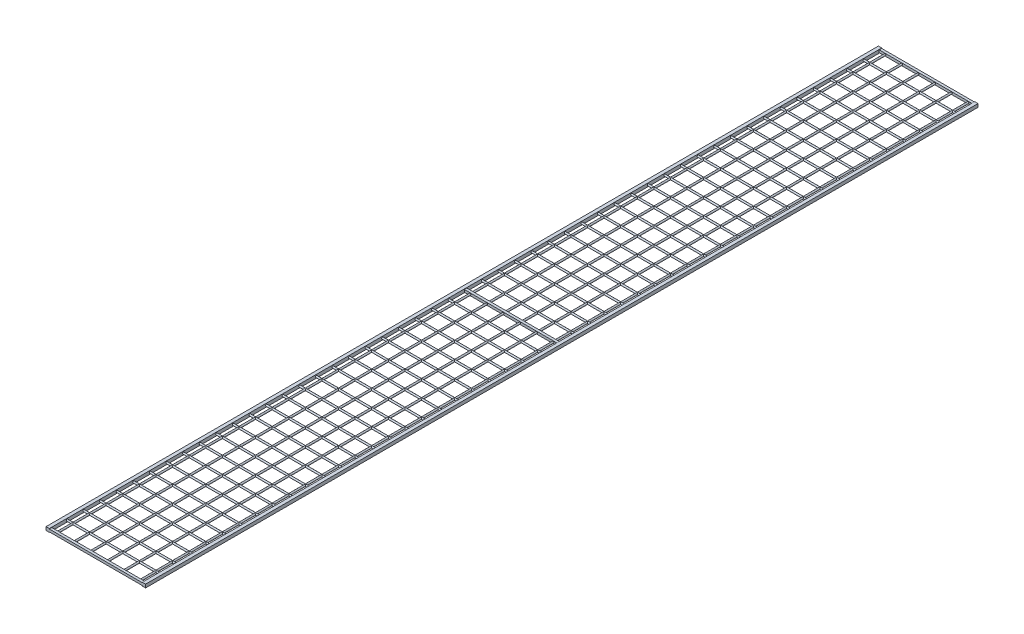
SolidWorks part; units mm, degrees
ref_plane "Piano frontale" through (0, 0, 0) normal (0, 0, 1) x (1, 0, 0)
ref_plane "Piano superiore" through (0, 0, 0) normal (0, 1, 0) x (1, 0, 0)
ref_plane "Piano destro" through (0, 0, 0) normal (1, 0, 0) x (0, 0, -1)
sketch "Schizzo2" plane through (0, 0, 0) normal (0, 0, 1) x (1, 0, 0)
  line L0 (0, 0) -> (5.716, 0) construction
  line L1 (0, 0) -> (50, 0) construction
  circle A0 centre (0, 0) radius 2.5
  circle A1 centre (50, 0) radius 2.5
  circle A2 centre (100, 0) radius 2.5
  circle A3 centre (150, 0) radius 2.5
  circle A4 centre (200, 0) radius 2.5
  circle A5 centre (250, 0) radius 2.5
  circle A6 centre (300, 0) radius 2.5
  circle A7 centre (350, 0) radius 2.5
  circle A8 centre (400, 0) radius 2.5
  circle A9 centre (450, 0) radius 2.5
  circle A10 centre (500, 0) radius 2.5
  circle A11 centre (550, 0) radius 2.5
  circle A12 centre (600, 0) radius 2.5
  circle A13 centre (650, 0) radius 2.5
  circle A14 centre (700, 0) radius 2.5
  circle A15 centre (750, 0) radius 2.5
  circle A16 centre (800, 0) radius 2.5
  circle A17 centre (850, 0) radius 2.5
  circle A18 centre (900, 0) radius 2.5
  dimension "D1" = 50
  dimension "D2" = 19
extrude "Estrusione-Estrusione1" add sketch "Schizzo2" along normal blind 2500 contours A0
sketch "Schizzo3" plane through (0, 0, 0) normal (1, 0, 0) x (0, 0, -1)
  line L0 (0, 0) -> (-50, 0) construction
  circle A0 centre (0, 0) radius 2.5
  circle A1 centre (-50, 0) radius 2.5
  circle A2 centre (-100, 0) radius 2.5
  circle A3 centre (-150, 0) radius 2.5
  circle A4 centre (-200, 0) radius 2.5
  circle A5 centre (-250, 0) radius 2.5
  circle A6 centre (-300, 0) radius 2.5
  circle A7 centre (-350, 0) radius 2.5
  circle A8 centre (-400, 0) radius 2.5
  circle A9 centre (-450, 0) radius 2.5
  circle A10 centre (-500, 0) radius 2.5
  circle A11 centre (-550, 0) radius 2.5
  circle A12 centre (-600, 0) radius 2.5
  circle A13 centre (-650, 0) radius 2.5
  circle A14 centre (-700, 0) radius 2.5
  circle A15 centre (-750, 0) radius 2.5
  circle A16 centre (-800, 0) radius 2.5
  circle A17 centre (-850, 0) radius 2.5
  circle A18 centre (-900, 0) radius 2.5
  circle A19 centre (-950, 0) radius 2.5
  circle A20 centre (-1000, 0) radius 2.5
  circle A21 centre (-1050, 0) radius 2.5
  circle A22 centre (-1100, 0) radius 2.5
  circle A23 centre (-1150, 0) radius 2.5
  circle A24 centre (-1200, 0) radius 2.5
  circle A25 centre (-1250, 0) radius 2.5
  circle A26 centre (-1300, 0) radius 2.5
  circle A27 centre (-1350, 0) radius 2.5
  circle A28 centre (-1400, 0) radius 2.5
  circle A29 centre (-1450, 0) radius 2.5
  circle A30 centre (-1500, 0) radius 2.5
  circle A31 centre (-1550, 0) radius 2.5
  circle A32 centre (-1600, 0) radius 2.5
  circle A33 centre (-1650, 0) radius 2.5
  circle A34 centre (-1700, 0) radius 2.5
  circle A35 centre (-1750, 0) radius 2.5
  circle A36 centre (-1800, 0) radius 2.5
  circle A37 centre (-1850, 0) radius 2.5
  circle A38 centre (-1900, 0) radius 2.5
  circle A39 centre (-1950, 0) radius 2.5
  circle A40 centre (-2000, 0) radius 2.5
  circle A41 centre (-2050, 0) radius 2.5
  circle A42 centre (-2100, 0) radius 2.5
  circle A43 centre (-2150, 0) radius 2.5
  circle A44 centre (-2200, 0) radius 2.5
  circle A45 centre (-2250, 0) radius 2.5
  circle A46 centre (-2300, 0) radius 2.5
  circle A47 centre (-2350, 0) radius 2.5
  circle A48 centre (-2400, 0) radius 2.5
  circle A49 centre (-2450, 0) radius 2.5
  circle A50 centre (-2500, 0) radius 2.5
  dimension "D1" = 51
  dimension "D2" = 50
extrude "Estrusione-Estrusione2" add sketch "Schizzo3" against normal blind 27.5 and the other way blind 922.5
sketch "Schizzo5" plane through (-27.5, 0, 0) normal (-1, 0, 0) x (0, 0, 1)
  line L0 (1246.25, 3.75) -> (1253.75, 3.75)
  line L1 (-3.75, 3.75) -> (3.75, 3.75)
  line L2 (-3.75, 3.75) -> (-3.75, -3.75)
  line L3 (-3.75, -3.75) -> (3.75, -3.75)
  line L4 (3.75, 3.75) -> (3.75, -3.75)
  line L5 (1246.25, 3.75) -> (1246.25, -3.75)
  line L6 (1246.25, -3.75) -> (1253.75, -3.75)
  line L7 (1253.75, 3.75) -> (1253.75, -3.75)
  line L8 (2496.25, 3.75) -> (2503.75, 3.75)
  line L9 (2496.25, 3.75) -> (2496.25, -3.75)
  line L10 (2496.25, -3.75) -> (2503.75, -3.75)
  line L11 (2503.75, 3.75) -> (2503.75, -3.75)
  line L12 (-3.75, 3.75) -> (1246.25, 3.75) construction
  dimension "D1" = 7.5
  dimension "D2" = 7.5
  dimension "D3" = 3.75
  dimension "D4" = 3.75
  dimension "D5" = 1250
extrude "Estrusione-Estrusione3" add sketch "Schizzo5" against normal up to surface (950 mm away)
sketch "Schizzo7" plane through (0, 0, -3.75) normal (0, 0, -1) x (-1, 0, 0)
  line L0 (27.5, 3.75) -> (27.5, -3.75) construction
  line L1 (27.5, -5) -> (17.5, -5)
  line L2 (27.5, -5) -> (27.5, 5)
  line L3 (27.5, 5) -> (17.5, 5)
  line L4 (17.5, -5) -> (17.5, 5)
  line L5 (-922.5, -3.75) -> (27.5, -3.75) construction
  line L6 (-912.5, -5) -> (-912.5, 5)
  line L7 (-912.5, -5) -> (-922.5, -5)
  line L8 (-922.5, -5) -> (-922.5, 5)
  line L9 (-912.5, 5) -> (-922.5, 5)
  dimension "D1" = 10
  dimension "D2" = 10
  dimension "D3" = 10
  dimension "D4" = 1.25
  dimension "D5" = 950
extrude "Estrusione-Estrusione4" add sketch "Schizzo7" against normal up to surface (2507.5 mm away)
sketch "Schizzo8" plane through (0, 0, 2503.75) normal (0, 0, 1) x (1, 0, 0)
  line L0 (-27.5, -5) -> (-27.5, 5) construction
  line L1 (272.5, 24.5677) -> (945.6323, 24.5677)
  line L2 (272.5, 24.5677) -> (272.5, -49.7845)
  line L3 (272.5, -49.7845) -> (945.6323, -49.7845)
  line L4 (945.6323, 24.5677) -> (945.6323, -49.7845)
  dimension "D1" = 300
extrude "Taglio-Estrusione1" cut sketch "Schizzo8" against normal up to surface (2507.5 mm away)
sketch "Schizzo9" plane through (0, 0, 2503.75) normal (0, 0, 1) x (1, 0, 0)
  line L1 (262.5, 5) -> (272.5, 5)
  line L2 (262.5, 5) -> (262.5, -5)
  line L3 (262.5, -5) -> (272.5, -5)
  line L4 (272.5, 5) -> (272.5, -5)
  line L7 (272.5, 3.75) -> (-17.5, 3.75) construction
  line L8 (272.5, 3.75) -> (272.5, -3.75) construction
  dimension "D1" = 10
  dimension "D2" = 10
  dimension "D3" = 1.25
  dimension "D4" = 0
extrude "Estrusione-Estrusione5" add sketch "Schizzo9" against normal up to surface (2507.5 mm away)
